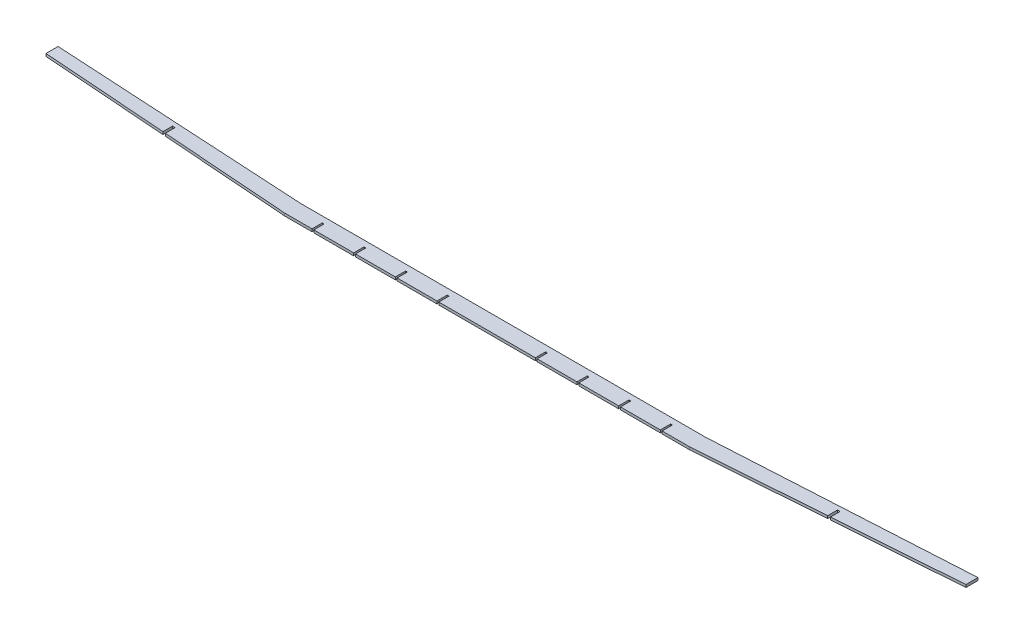
SolidWorks part; units mm, degrees
ref_plane "Front Plane" through (0, 0, 0) normal (0, 0, 1) x (1, 0, 0)
ref_plane "Top Plane" through (0, 0, 0) normal (0, 1, 0) x (1, 0, 0)
ref_plane "Right Plane" through (0, 0, 0) normal (1, 0, 0) x (0, 0, -1)
sketch "Sketch1" plane through (0, 0, 0) normal (0, 1, 0) x (1, 0, 0)
  line L0 (335.3, -13.5) -> (762, 17.8)
  line L1 (0, 13.5) -> (335.3, 13.5)
  line L2 (0, 13.5) -> (0, -13.5)
  line L3 (0, -13.5) -> (335.3, -13.5)
  line L4 (335.3, 13.5) -> (335.3, -13.5) construction
  line L5 (762, 17.8) -> (762, 37.8)
  line L6 (762, 37.8) -> (335.3, 13.5)
  line L7 (335.3, 0) -> (762, 27.8) construction
  point P4 (0, 0)
  dimension "D1" = 27
  dimension "D2" = 335.3
  dimension "D3" = 426.7
  dimension "D4" = 20
  dimension "D5" = 31.3
  dimension "D6" = 3.728
extrude "Boss-Extrude1" add sketch "Sketch1" along normal blind 4.3
sketch "Sketch2" plane through (0, 4.3, 0) normal (0, 1, 0) x (1, 0, 0)
  line L0 (0, -13.5) -> (335.3, -13.5) construction
  line L1 (80, -13.5) -> (83, -13.5)
  line L2 (80, -13.5) -> (80, 3.5)
  line L3 (80, 3.5) -> (83, 3.5)
  line L4 (83, -13.5) -> (83, 3.5)
  line L5 (0, 13.5) -> (0, -13.5) construction
  line L6 (149, -13.5) -> (149, 3.5)
  line L7 (149, -13.5) -> (152, -13.5)
  line L8 (152, -13.5) -> (152, 3.5)
  line L9 (149, 3.5) -> (152, 3.5)
  line L10 (218, -13.5) -> (218, 3.5)
  line L11 (218, -13.5) -> (221, -13.5)
  line L12 (221, -13.5) -> (221, 3.5)
  line L13 (218, 3.5) -> (221, 3.5)
  line L14 (287, -13.5) -> (287, 3.5)
  line L15 (287, -13.5) -> (290, -13.5)
  line L16 (290, -13.5) -> (290, 3.5)
  line L17 (287, 3.5) -> (290, 3.5)
  line L18 (335.3, -13.5) -> (762, -13.5) construction
  line L19 (762, 17.8) -> (762, -13.5) construction
  line L20 (335.3, -13.5) -> (762, 17.8) construction
  line L21 (548.66, 2.1507) -> (552.96, 2.1507)
  line L22 (548.66, 2.1507) -> (548.66, 18.3507)
  line L23 (548.66, 18.3507) -> (552.96, 18.3507)
  line L24 (552.96, 2.1507) -> (552.96, 18.3507)
  dimension "D1" = 17
  dimension "D2" = 3
  dimension "D3" = 80
  dimension "D5" = 69
  dimension "D6" = 16.2
  dimension "D7" = 4.3
  dimension "D8" = 213.36
  dimension "D4" = 4
extrude "Cut-Extrude1" cut sketch "Sketch2" against normal through all both
mirror "Mirror1" about plane through (0, 0, 0) normal (1, 0, 0) of "Boss-Extrude1", "Cut-Extrude1"
